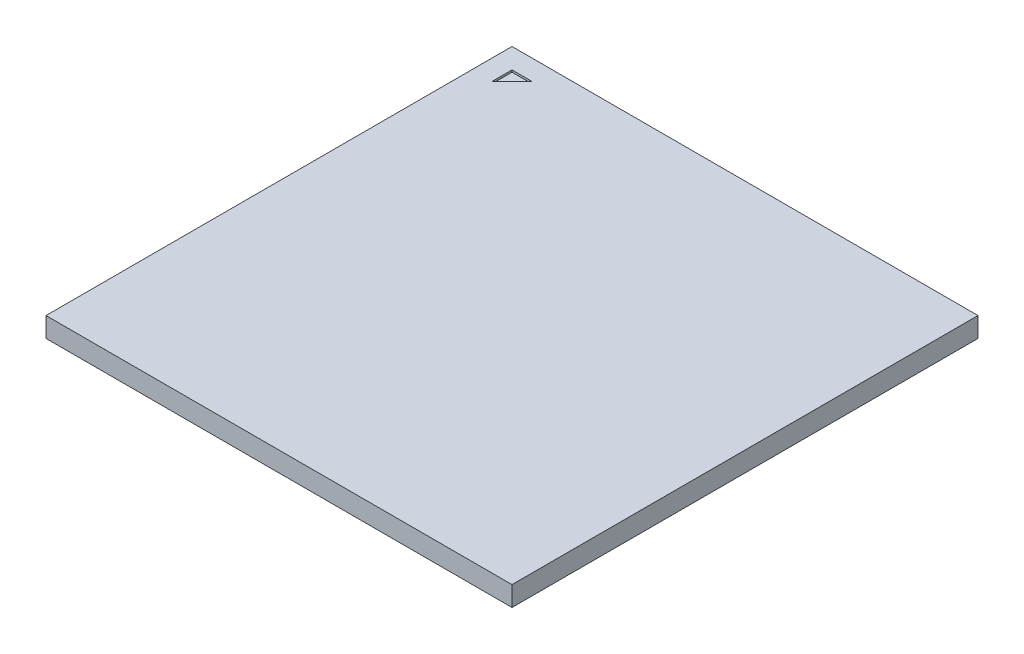
SolidWorks part; units mm, degrees
ref_plane "Front Plane" through (0, 0, 0) normal (0, 0, 1) x (1, 0, 0)
ref_plane "Top Plane" through (0, 0, 0) normal (0, 1, 0) x (1, 0, 0)
ref_plane "Right Plane" through (0, 0, 0) normal (1, 0, 0) x (0, 0, -1)
sketch "Sketch1" plane through (0, 0, 0) normal (0, 1, 0) x (1, 0, 0)
  line L1 (-11.5, -11.5) -> (11.5, -11.5)
  line L2 (-11.5, -11.5) -> (-11.5, 11.5)
  line L3 (-11.5, 11.5) -> (11.5, 11.5)
  line L4 (11.5, -11.5) -> (11.5, 11.5)
  line L5 (-11.5, -11.5) -> (11.5, 11.5) construction
  line L6 (-11.5, 11.5) -> (11.5, -11.5) construction
  point P0 (0, 0)
  dimension "D1" = 23
extrude "Boss-Extrude1" add sketch "Sketch1" along normal blind 0.98
sketch "Sketch2" plane through (0, 0.98, 0) normal (0, 1, 0) x (1, 0, 0)
  line L0 (-10.5, 10.5) -> (-9.5, 10.5)
  line L1 (-9.5, 10.5) -> (-10.5, 9.5)
  line L2 (-10.5, 9.5) -> (-10.5, 10.5)
  line L3 (-11.5, 11.5) -> (-11.5, -11.5) construction
  line L4 (11.5, 11.5) -> (-11.5, 11.5) construction
  dimension "D1" = 1
  dimension "D2" = 1
  dimension "D3" = 1
extrude "Cut-Extrude1" cut sketch "Sketch2" against normal blind 0.1
